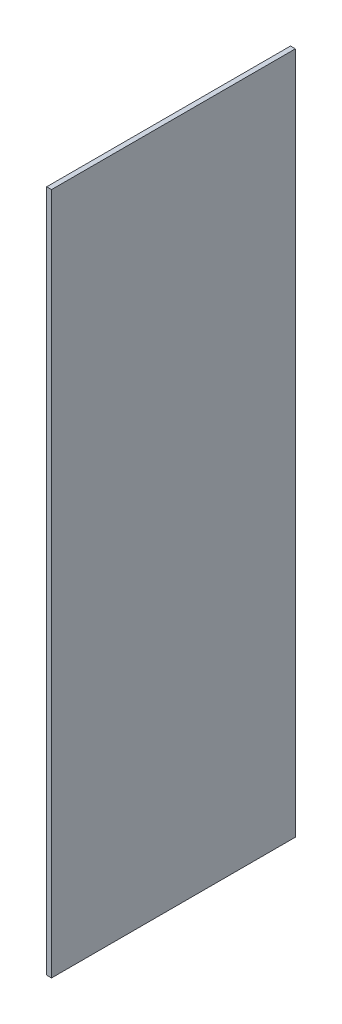
SolidWorks part; units mm, degrees
ref_plane "Front Plane" through (0, 0, 0) normal (0, 0, 1) x (1, 0, 0)
ref_plane "Top Plane" through (0, 0, 0) normal (0, 1, 0) x (1, 0, 0)
ref_plane "Right Plane" through (0, 0, 0) normal (1, 0, 0) x (0, 0, -1)
sketch "Sketch1" plane through (0, 0, 0) normal (0, 0, 1) x (1, 0, 0)
  line L1 (0, 0) -> (0.1, 0)
  line L2 (0, 0) -> (0, 14)
  line L3 (0, 14) -> (0.1, 14)
  line L4 (0.1, 0) -> (0.1, 14)
  dimension "D2" = 0.1
extrude "Boss-Extrude1" add sketch "Sketch1" along normal blind 5
equation "\"A.L\"= 0.07m"
equation "\"A.h\"= 0.007m"
equation "\"A.d\"= 0.005m"
equation "\"A.delta\"= 45.0001"
equation "\"A.w\"= 0m"
equation "\"A.v\"= 0.013m"
equation "\"A.s\"= 0.014m"
equation "\"A.t\"= 0.007m"
equation "\"B.L\"= 0.065m"
equation "\"B.h\"= 0.008m"
equation "\"B.s\"= 0.016m"
equation "\"B.t\"= 0.008m"
equation "\"C.h\"= 0.0065m"
equation "\"C.d\"= 0.005m"
equation "\"C.L\"= 0.05m"
equation "\"C.wmax\"= 0.003m"
equation "\"D.L\"= 0.06m"
equation "\"D.h\"= 0.008m"
equation "\"D.s\"= 0.012m"
equation "\"D.t\"= 0.008m"
equation "\"a_h\"= 0.0001m"
equation "\"a_d\"= 0.005m"
equation "\"a_L\"= 0.008m"
equation "\"b_h\"= 0.0004m"
equation "\"b_d\"= 0.005m"
equation "\"b_L\"= 0.008m"
equation "\"c_h\"= 0.0001m"
equation "\"c_d\"= 0.005m"
equation "\"c_L\"= 0.01m"
equation "\"d_h\"= 0.0001m"
equation "\"d_d\"= 0.005m"
equation "\"d_L\"= 0.01m"
equation "\"S.h\"= 0.015m"
equation "\"S.L\"= 0.09175m"
equation "\"D1@Sketch1\"=\"a_L\"+0.006"
equation "\"D2@Sketch1\"=\"a_h\""
equation "\"D1@Boss-Extrude1\"=\"a_d\""
